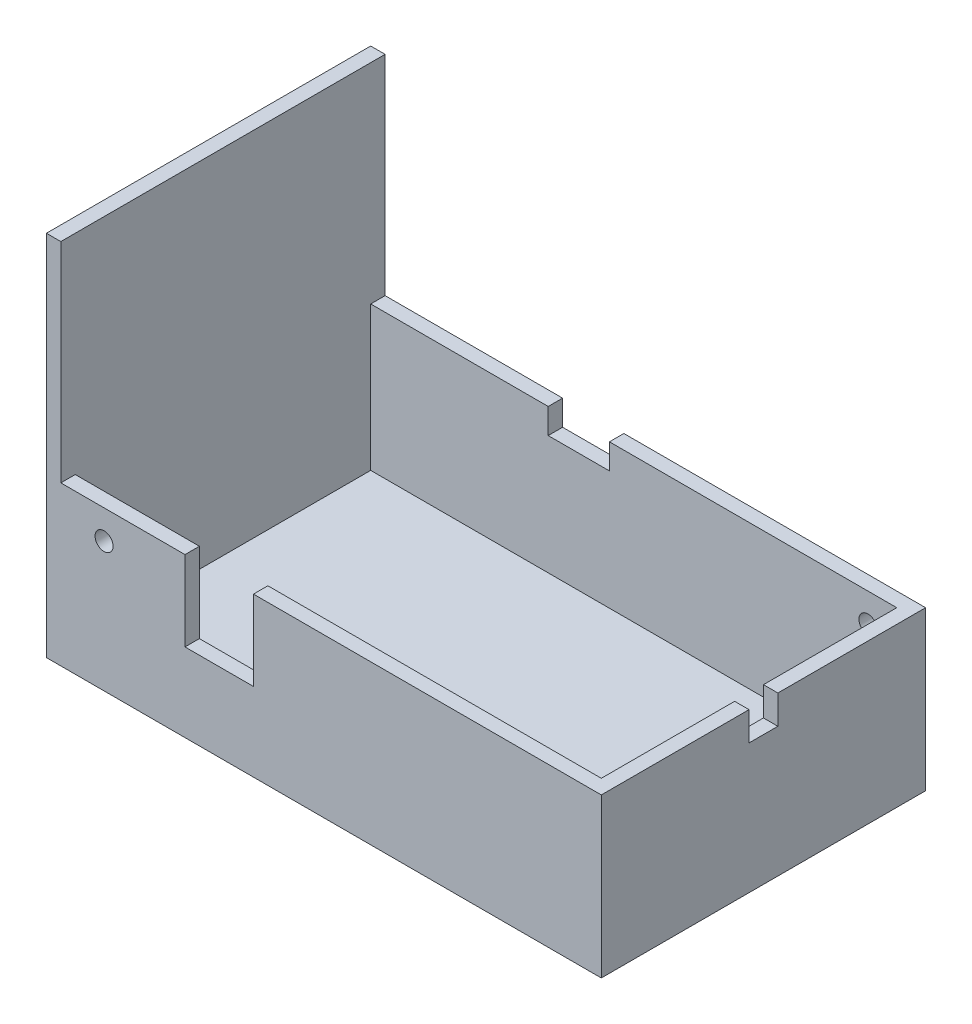
SolidWorks part; units mm, degrees
ref_plane "Front Plane" through (0, 0, 0) normal (0, 0, 1) x (1, 0, 0)
ref_plane "Top Plane" through (0, 0, 0) normal (0, 1, 0) x (1, 0, 0)
ref_plane "Right Plane" through (0, 0, 0) normal (1, 0, 0) x (0, 0, -1)
sketch "Sketch1" plane through (0, 0, 0) normal (0, 1, 0) x (1, 0, 0)
  line L1 (-38.5, -22.5) -> (38.5, -22.5)
  line L2 (-38.5, -22.5) -> (-38.5, 22.5)
  line L3 (-38.5, 22.5) -> (38.5, 22.5)
  line L4 (38.5, -22.5) -> (38.5, 22.5)
  line L5 (-38.5, -22.5) -> (38.5, 22.5) construction
  line L6 (-38.5, 22.5) -> (38.5, -22.5) construction
  point P0 (0, 0)
  dimension "D1" = 77
  dimension "D2" = 45
extrude "Boss-Extrude1" add sketch "Sketch1" along normal blind 2
sketch "Sketch2" plane through (0, 2, 0) normal (0, 1, 0) x (1, 0, 0)
  line L0 (-38.5, -22.5) -> (-38.5, 22.5)
  line L1 (-38.5, 22.5) -> (38.5, 22.5)
  line L2 (38.5, 22.5) -> (-38.5, 22.5) construction
  line L3 (38.5, -22.5) -> (38.5, 22.5) construction
  line L4 (38.5, 22.5) -> (38.5, -22.5)
  line L5 (38.5, -22.5) -> (-38.5, -22.5)
  line L6 (-36.5, 20.5) -> (36.5, 20.5)
  line L7 (36.5, 20.5) -> (36.5, -20.5)
  line L8 (36.5, -20.5) -> (-36.5, -20.5)
  line L9 (-36.5, -20.5) -> (-36.5, 20.5)
  dimension "D1" = 2
  dimension "D2" = 2
  dimension "D3" = 2
  dimension "D4" = 2
extrude "Boss-Extrude2" add sketch "Sketch2" along normal blind 20
sketch "Sketch3" plane through (0, 22, 0) normal (0, 1, 0) x (1, 0, 0)
  line L0 (38.5, 22.5) -> (-38.5, 22.5) construction
  line L1 (-38.5, -22.5) -> (-36.5, -22.5)
  line L2 (-38.5, -22.5) -> (-38.5, 22.5)
  line L3 (-38.5, 22.5) -> (-36.5, 22.5)
  line L4 (-36.5, -22.5) -> (-36.5, 22.5)
  line L5 (-38.5, -22.5) -> (-36.5, 22.5) construction
  line L6 (-38.5, 22.5) -> (-36.5, -22.5) construction
  line L7 (-36.5, 20.5) -> (-36.5, -20.5) construction
  point P4 (-37.5, 0)
extrude "Boss-Extrude3" add sketch "Sketch3" along normal blind 29
sketch "Sketch4" plane through (0, 0, -22.5) normal (0, 0, -1) x (-1, 0, 0)
  line L0 (-38.5, 22) -> (36.5, 22) construction
  line L1 (-38.5, 22) -> (-38.5, 0) construction
  circle A0 centre (-32.5, 18) radius 1.25
  dimension "D1" = 2.5
  dimension "D2" = 4
  dimension "D3" = 6
extrude "Cut-Extrude1" cut sketch "Sketch4" against normal up to surface (2 mm away) up to face at (0, 12, -20.5)
sketch "Sketch5" plane through (0, 0, 22.5) normal (0, 0, 1) x (1, 0, 0)
  line L0 (-36.5, 22) -> (38.5, 22) construction
  line L1 (-36.5, 51) -> (-36.5, 22) construction
  circle A0 centre (-30.5, 18) radius 1.25
  dimension "D1" = 2.5
  dimension "D2" = 4
  dimension "D3" = 6
extrude "Cut-Extrude2" cut sketch "Sketch5" against normal up to surface (2 mm away) up to face at (0, 12, 20.5)
sketch "Sketch6" plane through (0, 0, 22.5) normal (0, 0, 1) x (1, 0, 0)
  line L0 (-36.5, 22) -> (38.5, 22) construction
  line L1 (-19.27, 22) -> (-9.77, 22)
  line L2 (-19.27, 22) -> (-19.27, 10.9)
  line L3 (-19.27, 10.9) -> (-9.77, 10.9)
  line L4 (-9.77, 22) -> (-9.77, 10.9)
  line L5 (-19.27, 22) -> (-9.77, 10.9) construction
  line L6 (-19.27, 10.9) -> (-9.77, 22) construction
  line L7 (-36.5, 51) -> (-36.5, 22) construction
  point P4 (-14.52, 16.45)
  dimension "D1" = 9.5
  dimension "D2" = 11.1
  dimension "D3" = 17.23
extrude "Cut-Extrude3" cut sketch "Sketch6" against normal up to surface (2 mm away) up to face at (-31.75, 18, 20.5)
sketch "Sketch7" plane through (0, 0, -22.5) normal (0, 0, -1) x (-1, 0, 0)
  line L0 (-38.5, 22) -> (36.5, 22) construction
  line L1 (3.37, 22) -> (11.87, 22)
  line L2 (3.37, 22) -> (3.37, 18.5)
  line L3 (3.37, 18.5) -> (11.87, 18.5)
  line L4 (11.87, 22) -> (11.87, 18.5)
  line L5 (3.37, 22) -> (11.87, 18.5) construction
  line L6 (3.37, 18.5) -> (11.87, 22) construction
  line L7 (36.5, 51) -> (36.5, 22) construction
  point P4 (7.62, 20.25)
  dimension "D1" = 8.5
  dimension "D2" = 3.5
  dimension "D3" = 24.63
extrude "Cut-Extrude4" cut sketch "Sketch7" against normal up to surface (2 mm away) contours L3 L4 L1 L2 up to face at (33.75, 18, -20.5)
sketch "Sketch8" plane through (38.5, 0, 0) normal (1, 0, 0) x (0, 0, -1)
  line L0 (-22.5, 22) -> (22.5, 22) construction
  line L1 (-2, 22) -> (2, 22)
  line L2 (-2, 22) -> (-2, 18)
  line L3 (-2, 18) -> (2, 18)
  line L4 (2, 22) -> (2, 18)
  line L5 (-2, 22) -> (2, 18) construction
  line L6 (-2, 18) -> (2, 22) construction
  line L7 (-22.5, 0) -> (22.5, 0) construction
  point P4 (0, 20)
  point P10 (0, 0)
  dimension "D1" = 4
  dimension "D2" = 4
extrude "Cut-Extrude5" cut sketch "Sketch8" against normal up to surface (2 mm away) up to face at (36.5, 12, 0)
